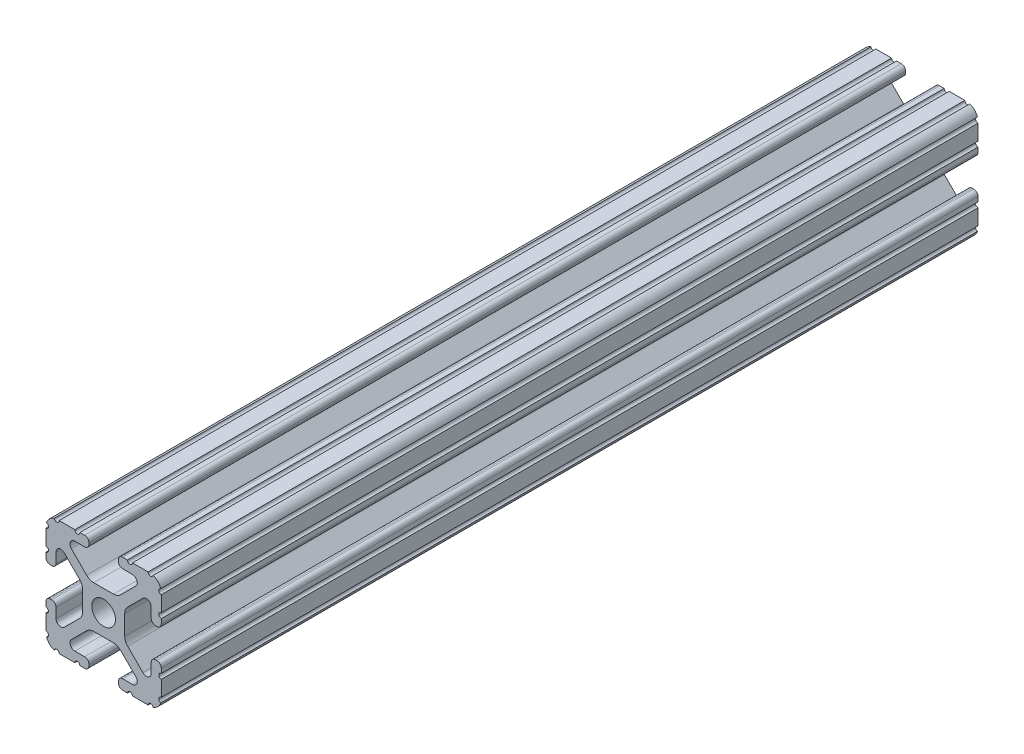
SolidWorks part; units mm, degrees
ref_plane "Front Plane" through (0, 0, 0) normal (0, 0, 1) x (1, 0, 0)
ref_plane "Top Plane" through (0, 0, 0) normal (0, 1, 0) x (1, 0, 0)
ref_plane "Right Plane" through (0, 0, 0) normal (1, 0, 0) x (0, 0, -1)
sketch "Sketch2" plane through (0, 0, 0) normal (0, 0, 1) x (1, 0, 0)
  line L0 (0, 12.7) -> (0, -12.7) construction
  line L1 (-12.7, 0) -> (12.7, 0) construction
  line L2 (3.2512, -12.7) -> (12.7, -12.7)
  line L3 (12.7, -12.7) -> (12.7, -3.2512)
  line L4 (3.2512, -12.7) -> (3.2512, -10.4902)
  line L5 (3.2512, -10.4902) -> (8.9276, -10.4902)
  line L6 (8.9276, -10.4902) -> (3.0856, -4.6482)
  line L7 (0, 0) -> (12.7, -12.7) construction
  line L8 (12.7, -3.2512) -> (10.4902, -3.2512)
  line L9 (10.4902, -3.2512) -> (10.4902, -8.9276)
  line L10 (10.4902, -8.9276) -> (4.6482, -3.0856)
  circle A0 centre (0, 0) radius 2.6035
  arc A1 (6.3485, -10.4902) -> (7.1039, -8.6665) centre (6.3485, -9.4219) ccw construction
  point P8 (0, -4.6482)
  dimension "Center Hole Diameter" = 5.207
  dimension "Rail Height" = 25.4
  dimension "Rail Width" = 25.4
  dimension "T-Slot Width" = 6.5024
  dimension "Slot Inner Width" = 14.8336
  dimension "Thickness" = 2.2098
  dimension "Slot Depth" = 5.842
  dimension "D1" = 2.2098
sketch "Sketch3" plane through (0, 0, 0) normal (1, 0, 0) x (0, 0, -1)
  line L0 (-228.6, -12.7) -> (228.6, -12.7) construction
  line L1 (-205.74, 0) -> (205.74, 0) construction
  dimension "Length" = 457.2
  dimension "D1" = 411.48
sketch "Sketch4" plane through (0, 0, 0) normal (0, 0, 1) x (1, 0, 0)
  line L0 (4.1904, -12.7) -> (10.1173, -12.7)
  line L1 (3.2512, -12.7) -> (12.7, -12.7) construction
  line L2 (3.2512, -12.7) -> (3.2512, -10.4902) construction
  line L3 (3.2512, -10.4902) -> (8.9276, -10.4902) construction
  line L4 (3.2512, -11.4294) -> (3.2512, -11.7608)
  line L5 (4.1904, -10.4902) -> (6.3485, -10.4902)
  line L6 (0, -4.6482) -> (2.164, -4.6482)
  line L7 (8.9276, -10.4902) -> (3.0856, -4.6482) construction
  line L8 (3.7373, -5.2999) -> (7.1039, -8.6665)
  line L9 (12.7, -12.7) -> (12.7, -3.2512) construction
  line L10 (10.4902, -8.9276) -> (4.6482, -3.0856) construction
  line L11 (10.4902, -3.2512) -> (10.4902, -8.9276) construction
  line L12 (10.4902, -6.3485) -> (10.4902, -4.1904)
  line L13 (12.7, -3.2512) -> (10.4902, -3.2512) construction
  line L14 (11.4294, -3.2512) -> (11.7608, -3.2512)
  line L15 (12.7, -4.1904) -> (12.7, -10.1173)
  line L16 (8.6665, -7.1039) -> (5.2999, -3.7373)
  line L17 (4.6482, 0) -> (4.6482, -2.164)
  line L18 (-12.7, 0) -> (12.7, 0) construction
  line L19 (0, -4.6482) -> (0, -2.6035)
  line L20 (0, 12.7) -> (0, -12.7) construction
  line L21 (4.6482, 0) -> (2.6035, 0)
  arc A0 (3.2512, -11.7608) -> (4.1904, -12.7) centre (4.1904, -11.7608) ccw
  arc A2 (3.2512, -11.4294) -> (4.1904, -10.4902) centre (4.1904, -11.4294) cw
  arc A3 (6.3485, -10.4902) -> (7.1039, -8.6665) centre (6.3485, -9.4219) ccw
  arc A4 (2.164, -4.6482) -> (3.7373, -5.2999) centre (2.164, -6.8732) cw
  arc A5 (10.1173, -12.7) -> (12.7, -10.1173) centre (10.1173, -10.1173) ccw
  arc A6 (8.6665, -7.1039) -> (10.4902, -6.3485) centre (9.4219, -6.3485) ccw
  arc A7 (10.4902, -4.1904) -> (11.4294, -3.2512) centre (11.4294, -4.1904) cw
  arc A8 (11.7608, -3.2512) -> (12.7, -4.1904) centre (11.7608, -4.1904) cw
  arc A9 (5.2999, -3.7373) -> (4.6482, -2.164) centre (6.8732, -2.164) cw
  circle A10 centre (0, 0) radius 2.6035 construction
  arc A11 (0, -2.6035) -> (2.6035, 0) centre (0, 0) ccw
  dimension "D1" = 2.5827
  dimension "D2" = 2.225
  dimension "D3" = 0.9392
extrude "Boss-Extrude1" add sketch "Sketch4" along normal mid plane 180
sketch "Sketch5" plane through (0, 0, 0) normal (0, 0, 1) x (1, 0, 0)
  line L0 (3.2512, -12.7) -> (12.7, -12.7) construction
  line L1 (4.1904, -10.4902) -> (6.3485, -10.4902) construction
  line L3 (0, 0) -> (12.7, -12.7) construction
  line L4 (6.3485, -10.4902) -> (6.3485, -12.7) construction
  line L5 (8.9276, -10.4902) -> (3.0856, -4.6482) construction
  circle A0 centre (10.3562, -12.7) radius 0.5524
  circle A1 centre (5.796, -12.7) radius 0.5524
  circle A2 centre (12.7, -10.3562) radius 0.5524
  circle A3 centre (12.7, -5.796) radius 0.5524
  point P10 (5.2694, -10.4902)
  point P12 (9.4219, -6.3485)
  dimension "D1" = 1.1049
extrude "Cut-Extrude1" cut sketch "Sketch5" against normal through all both and the other way through all
mirror "Mirror1" about plane through (0, 0, 0) normal (1, 0, 0) of bodies 137 134
mirror "Mirror2" about plane through (0, 0, 0) normal (0, 1, 0) of bodies 135
equation "\"D1@Boss-Extrude1\"=\"Length@Sketch3\""
equation "\"D1@Sketch2\"=\"Thickness@Sketch2\""
equation "\"D2@Sketch4\"=\"Slot Inner Width@Sketch2\"*0.15"
equation "\"D1@Sketch4\"=\"D3@Sketch4\"*2.75"
equation "\"D3@Sketch4\"=\"Thickness@Sketch2\"*0.425"
equation "\"D1@Sketch5\"=\"Thickness@Sketch2\"*0.5"
equation "\"D1@Sketch3\"=\"Length@Sketch3\"*0.9"
